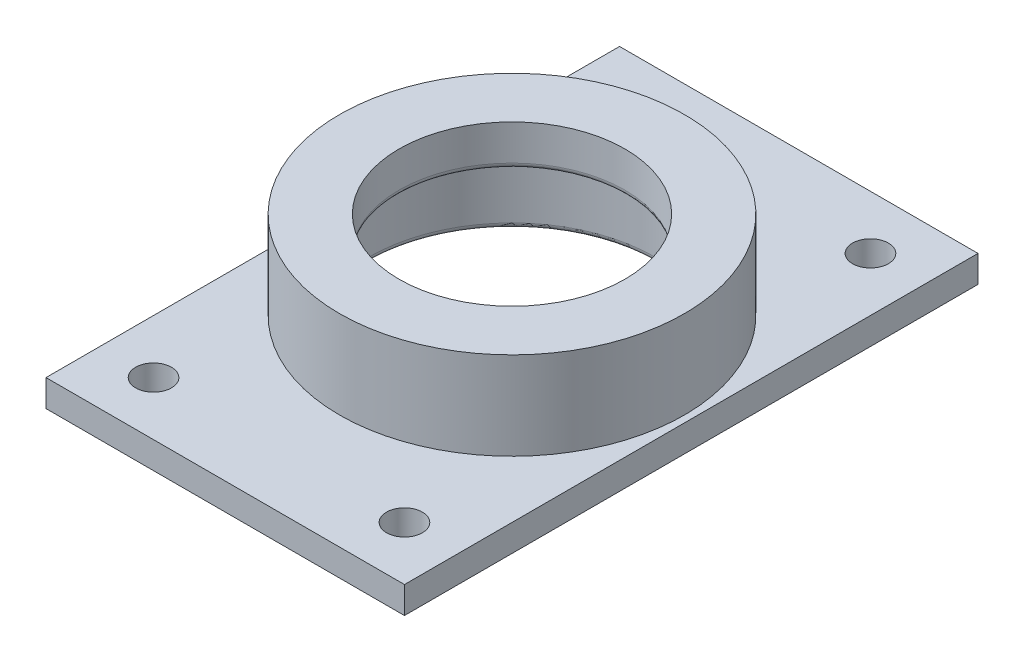
SolidWorks part; units mm, degrees
ref_plane "Front Plane" through (0, 0, 0) normal (0, 0, 1) x (1, 0, 0)
ref_plane "Top Plane" through (0, 0, 0) normal (0, 1, 0) x (1, 0, 0)
ref_plane "Right Plane" through (0, 0, 0) normal (1, 0, 0) x (0, 0, -1)
sketch "Sketch1" plane through (0, 0, 0) normal (0, 1, 0) x (1, 0, 0)
  circle A0 centre (0, 0) radius 30.55
extrude "Boss-Extrude1" add sketch "Sketch1" along normal blind 20.32
sketch "Sketch2" plane through (0, 0, 0) normal (0, -1, 0) x (1, 0, 0)
  circle A0 centre (0, 0) radius 25.404
extrude "Cut-Extrude1" cut sketch "Sketch2" against normal blind 13
sketch "Sketch3" plane through (0, 20.32, 0) normal (0, 1, 0) x (1, 0, 0)
  circle A0 centre (0, 0) radius 20
extrude "Cut-Extrude2" cut sketch "Sketch3" against normal through all
fillet "Fillet1" radius 1 1 edges at (0, 0, -25.404)
fillet "Fillet2" radius 1 1 edges at (0, 13, -20)
sketch "Sketch4" plane through (0, 0, 0) normal (0, -1, 0) x (1, 0, 0)
  line L0 (0, 50.8) -> (0, -50.8) construction
  line L1 (31.75, 50.8) -> (-31.75, 50.8)
  line L2 (31.75, 50.8) -> (31.75, -50.8)
  line L3 (31.75, -50.8) -> (-31.75, -50.8)
  line L4 (-31.75, 50.8) -> (-31.75, -50.8)
  line L5 (31.75, 50.8) -> (-31.75, -50.8) construction
  line L6 (31.75, -50.8) -> (-31.75, 50.8) construction
  line L7 (31.75, 0) -> (-31.75, 0) construction
  circle A0 centre (-22.225, 41.275) radius 3.175
  circle A1 centre (22.225, 41.275) radius 3.175
  circle A2 centre (22.225, -41.275) radius 3.175
  circle A3 centre (-22.225, -41.275) radius 3.175
  circle A4 centre (0, 0) radius 26.404
  point P0 (0, 0)
  dimension "D3" = 9.525
  dimension "D1" = 63.5
  dimension "D2" = 101.6
  dimension "D4" = 9.525
extrude "Boss-Extrude2" add sketch "Sketch4" against normal blind 4.7625
